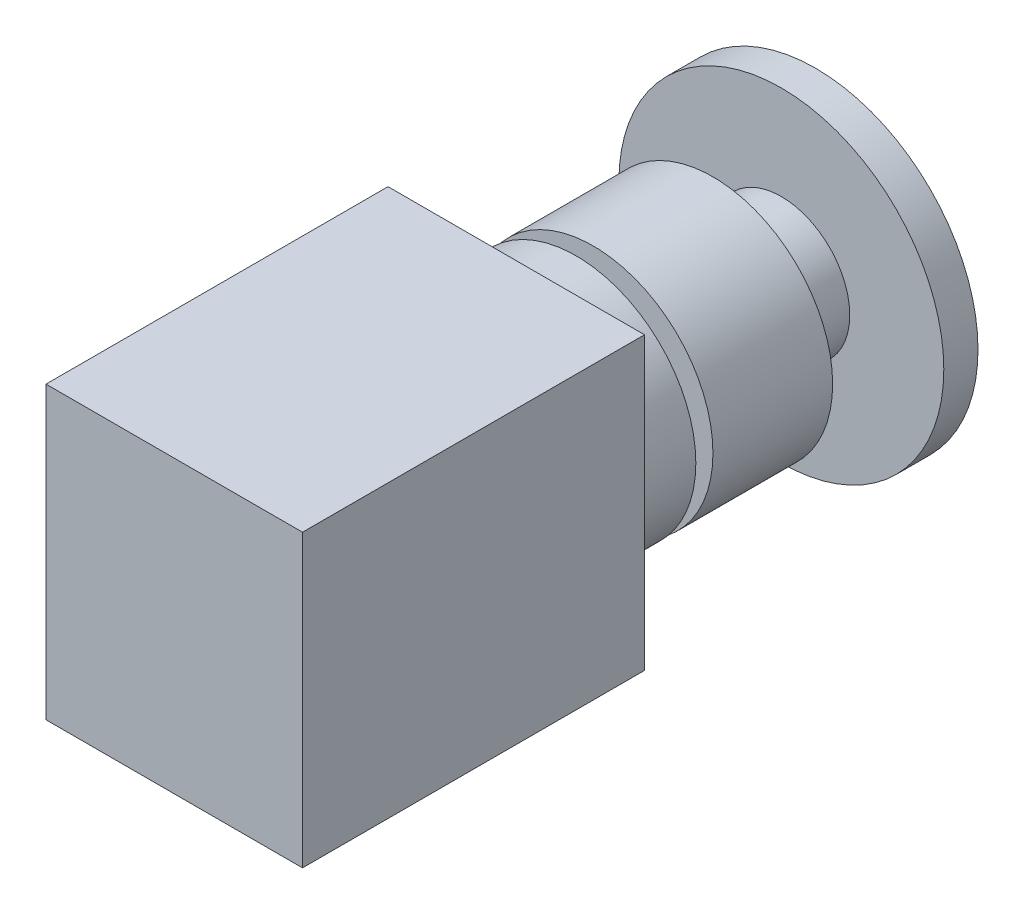
SolidWorks part; units mm, degrees
ref_plane "前视基准面" through (0, 0, 0) normal (0, 0, 1) x (1, 0, 0)
ref_plane "上视基准面" through (0, 0, 0) normal (0, 1, 0) x (1, 0, 0)
ref_plane "右视基准面" through (0, 0, 0) normal (1, 0, 0) x (0, 0, -1)
sketch "草图1" plane through (0, 0, 0) normal (0, 0, 1) x (1, 0, 0)
  circle A0 centre (0, 0) radius 19
extrude "凸台-拉伸1" add sketch "草图1" along normal blind 4
sketch "草图2" plane through (0, 0, 4) normal (0, 0, 1) x (1, 0, 0)
  circle A0 centre (0, 0) radius 8
extrude "凸台-拉伸2" add sketch "草图2" along normal blind 8
sketch "草图3" plane through (0, 0, 12) normal (0, 0, 1) x (1, 0, 0)
  circle A0 centre (0, 0) radius 14
extrude "凸台-拉伸3" add sketch "草图3" along normal blind 14
sketch "草图4" plane through (0, 0, 26) normal (0, 0, 1) x (1, 0, 0)
  circle A0 centre (0, 0) radius 11
extrude "凸台-拉伸4" add sketch "草图4" along normal blind 2
sketch "草图5" plane through (0, 0, 28) normal (0, 0, 1) x (1, 0, 0)
  circle A0 centre (0, 0) radius 14
extrude "凸台-拉伸5" add sketch "草图5" along normal blind 7
sketch "草图6" plane through (0, 0, 35) normal (0, 0, 1) x (1, 0, 0)
  line L1 (-15, 17) -> (15, 17)
  line L2 (-15, 17) -> (-15, -17)
  line L3 (-15, -17) -> (15, -17)
  line L4 (15, 17) -> (15, -17)
  line L5 (-15, 17) -> (15, -17) construction
  line L6 (-15, -17) -> (15, 17) construction
  point P0 (0, 0)
extrude "凸台-拉伸6" add sketch "草图6" along normal blind 40
